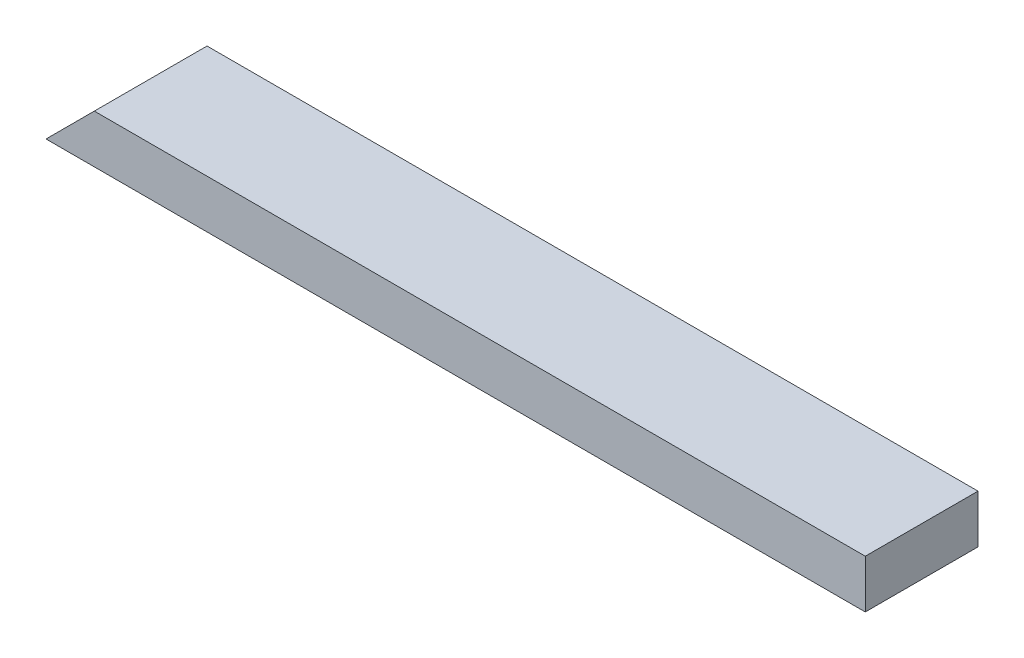
SolidWorks part; units mm, degrees
material "Pine"
ref_plane "Front Plane" through (0, 0, 0) normal (0, 0, 1) x (1, 0, 0)
ref_plane "Top Plane" through (0, 0, 0) normal (0, 1, 0) x (1, 0, 0)
ref_plane "Right Plane" through (0, 0, 0) normal (1, 0, 0) x (0, 0, -1)
sketch "Sketch1" plane through (0, 0, 0) normal (0, 1, 0) x (1, 0, 0)
  line L1 (0, 0) -> (646.1125, 0)
  line L2 (0, 0) -> (0, 88.9)
  line L3 (0, 88.9) -> (646.1125, 88.9)
  line L4 (646.1125, 0) -> (646.1125, 88.9)
  dimension "D1" = 88.9
  dimension "D2" = 646.1125
extrude "Boss-Extrude1" add sketch "Sketch1" along normal blind 38.1
sketch "Sketch2" plane through (0, 0, 0) normal (0, 0, 1) x (1, 0, 0)
  line L0 (0, 0) -> (38.1, 38.1)
  line L1 (0, 38.1) -> (646.1125, 38.1) construction
  line L2 (0, 38.1) -> (0, 0)
  line L6 (38.1, 38.1) -> (0, 38.1)
  dimension "D1" = 38.1
extrude "Cut-Extrude1" cut sketch "Sketch2" against normal through all
